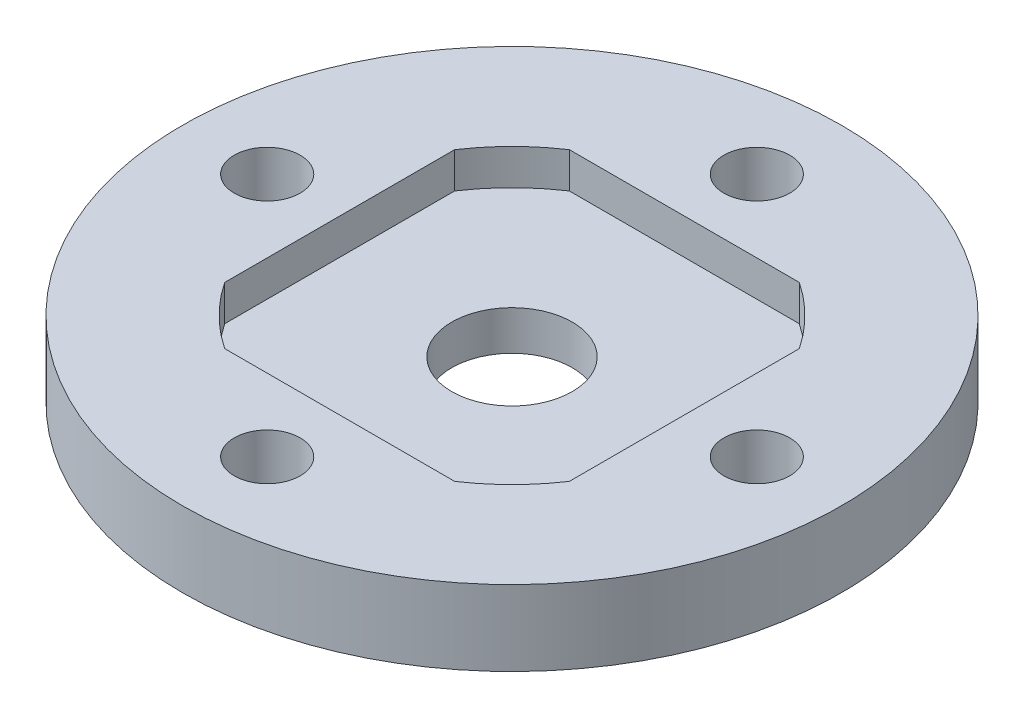
SolidWorks part; units mm, degrees
ref_plane "Спереди" through (0, 0, 0) normal (0, 0, 1) x (1, 0, 0)
ref_plane "Сверху" through (0, 0, 0) normal (0, 1, 0) x (1, 0, 0)
ref_plane "Справа" through (0, 0, 0) normal (1, 0, 0) x (0, 0, -1)
sketch "Эскиз1" plane through (0, 0, 0) normal (0, 1, 0) x (1, 0, 0)
  circle A0 centre (13.1065, -0.3415) radius 1.75
  circle A1 centre (0.1065, -13.3415) radius 1.75
  circle A2 centre (-12.8935, -0.3415) radius 1.75
  circle A3 centre (0.1065, 12.6585) radius 1.75
  circle A4 centre (0.1065, -0.3415) radius 17.5
  dimension "D1" = 35
  dimension "D2" = 3.5
  dimension "D3" = 3.5
  dimension "D4" = 3.5
  dimension "D5" = 3.5
extrude "Бобышка-Вытянуть1" add sketch "Эскиз1" along normal blind 4
sketch "Эскиз2" plane through (0, 4, 0) normal (0, 1, 0) x (1, 0, 0)
  circle A0 centre (0.1065, -0.3415) radius 3.2
  dimension "D1" = 6.4
extrude "Вырез-Вытянуть1" cut sketch "Эскиз2" against normal through all
sketch "Эскиз3" plane through (0, 4, 0) normal (0, 1, 0) x (1, 0, 0)
  line L1 (6.212, 8.8085) -> (-5.9991, 8.8085)
  line L2 (9.2565, 5.764) -> (9.2565, -6.447)
  line L3 (6.212, -9.4915) -> (-5.9991, -9.4915)
  line L4 (-9.0435, 5.764) -> (-9.0435, -6.447)
  line L5 (9.2565, 8.8085) -> (-9.0435, -9.4915) construction
  line L6 (9.2565, -9.4915) -> (-9.0435, 8.8085) construction
  arc A0 (-9.0435, -6.447) -> (-5.9991, -9.4915) centre (0.1065, -0.3415) ccw
  arc A1 (6.212, -9.4915) -> (9.2565, -6.447) centre (0.1065, -0.3415) ccw
  arc A2 (9.2565, 5.764) -> (6.212, 8.8085) centre (0.1065, -0.3415) ccw
  arc A3 (-5.9991, 8.8085) -> (-9.0435, 5.764) centre (0.1065, -0.3415) ccw
  point P0 (0.1065, -0.3415)
  dimension "D3" = 22
  dimension "D1" = 18.3
  dimension "D2" = 18.3
extrude "Вырез-Вытянуть2" cut sketch "Эскиз3" against normal blind 1.9
chamfer "Фаска1" distance 1.4 angle 45 4 edges at (0.1065, 0, 15.0915) (13.1065, 0, 2.0915) (-12.8935, 0, 2.0915) (0.1065, 0, -10.9085)
